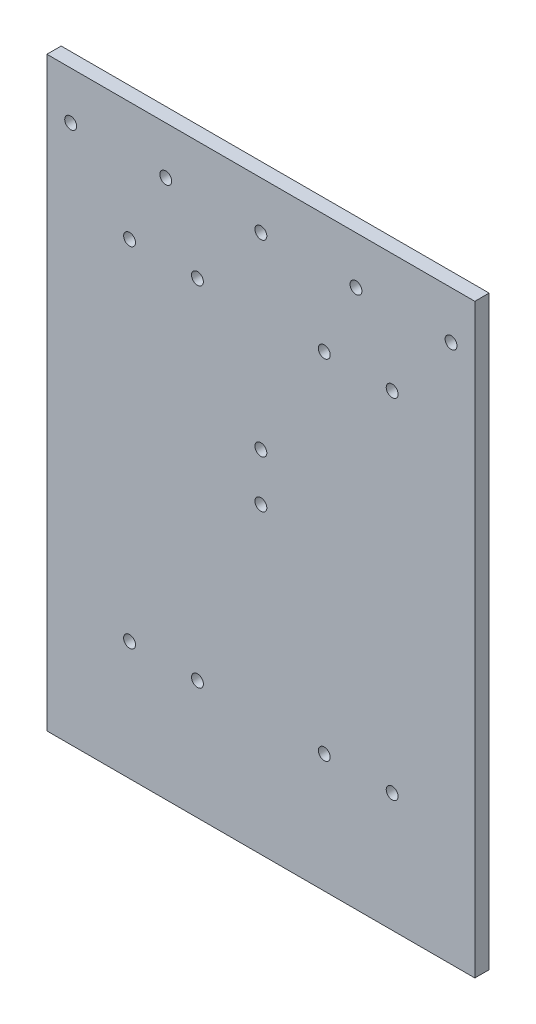
SolidWorks part; units mm, degrees
ref_plane "Front Plane" through (0, 0, 0) normal (0, 0, 1) x (1, 0, 0)
ref_plane "Top Plane" through (0, 0, 0) normal (0, 1, 0) x (1, 0, 0)
ref_plane "Right Plane" through (0, 0, 0) normal (1, 0, 0) x (0, 0, -1)
sketch "Sketch1" plane through (0, 0, 0) normal (0, 0, 1) x (1, 0, 0)
  line L0 (-55.225, 0) -> (-26.675, 0) construction
  line L1 (-90, 50) -> (90, 50)
  line L2 (-90, 50) -> (-90, -196.5)
  line L3 (-90, -196.5) -> (90, -196.5)
  line L4 (90, 50) -> (90, -196.5)
  line L5 (-26.675, 0) -> (26.675, 0) construction
  line L6 (26.675, 0) -> (55.225, 0) construction
  line L7 (-55.225, -146.5) -> (-26.675, -146.5) construction
  line L8 (-26.675, -146.5) -> (26.675, -146.5) construction
  line L9 (26.675, -146.5) -> (55.225, -146.5) construction
  line L10 (0, 0) -> (0, -146.5) construction
  line L11 (-80, 30) -> (-40, 30) construction
  line L12 (-40, 30) -> (0, 30) construction
  line L13 (0, 30) -> (40, 30) construction
  line L14 (40, 30) -> (80, 30) construction
  circle A0 centre (-55.225, 0) radius 2.5
  circle A1 centre (-26.675, 0) radius 2.5
  circle A2 centre (55.225, 0) radius 2.5
  circle A3 centre (26.675, 0) radius 2.5
  circle A4 centre (-55.225, -146.5) radius 2.5
  circle A5 centre (-26.675, -146.5) radius 2.5
  circle A6 centre (55.225, -146.5) radius 2.5
  circle A7 centre (26.675, -146.5) radius 2.5
  circle A8 centre (-80, 30) radius 2.5
  circle A9 centre (-40, 30) radius 2.5
  circle A10 centre (80, 30) radius 2.5
  circle A11 centre (40, 30) radius 2.5
  circle A12 centre (0, 30) radius 2.5
  circle A13 centre (0, -49) radius 2.5
  circle A14 centre (0, -69) radius 2.5
  point P35 (0, 50)
  dimension "D3" = 5
  dimension "D6" = 50
  dimension "D7" = 5
  dimension "D11" = 5
  dimension "D1" = 53.35
  dimension "D2" = 110.45
  dimension "D4" = 146.5
  dimension "D5" = 50
  dimension "D8" = 40
  dimension "D9" = 30
  dimension "D10" = 180
  dimension "D12" = 49
  dimension "D13" = 20
extrude "Boss-Extrude1" add sketch "Sketch1" along normal blind 6
